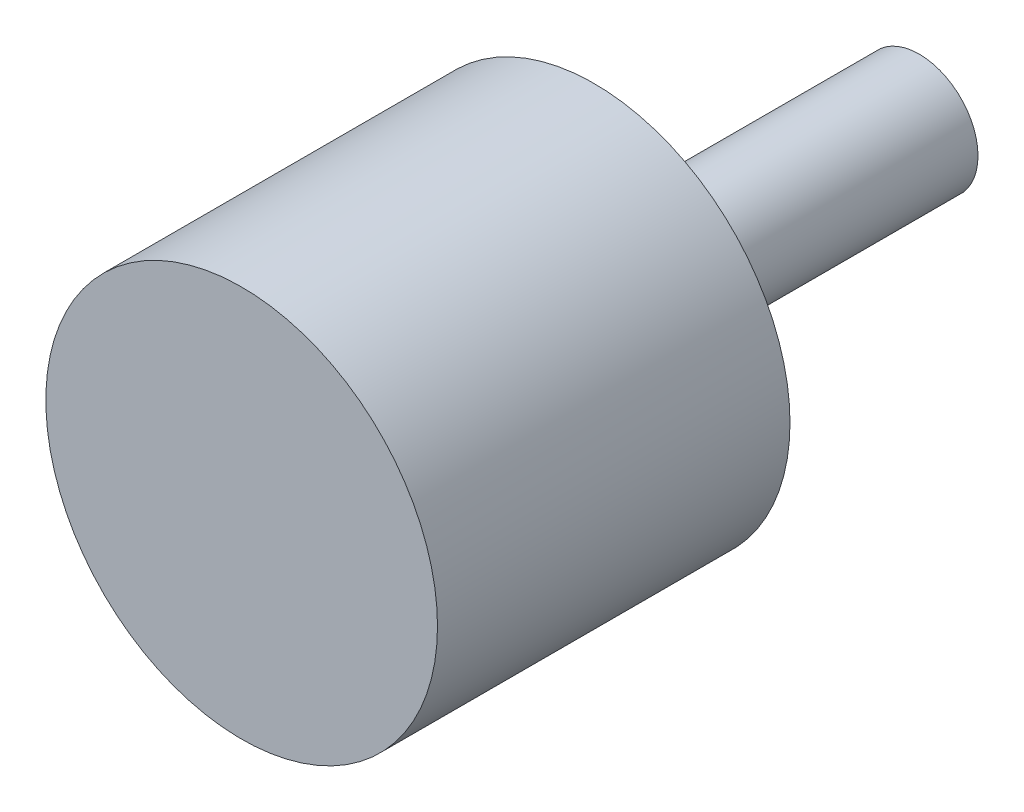
SolidWorks part; units mm, degrees
ref_plane "前视基准面" through (0, 0, 0) normal (0, 0, 1) x (1, 0, 0)
ref_plane "上视基准面" through (0, 0, 0) normal (0, 1, 0) x (1, 0, 0)
ref_plane "右视基准面" through (0, 0, 0) normal (1, 0, 0) x (0, 0, -1)
sketch "草图1" plane through (0, 0, 0) normal (0, 0, 1) x (1, 0, 0)
  circle A0 centre (0, 0) radius 5
  dimension "D1" = 10
extrude "凸台-拉伸1" add sketch "草图1" along normal blind 9
sketch "草图2" plane through (0, 0, 0) normal (0, 0, -1) x (-1, 0, 0)
  circle A0 centre (0, 0) radius 1.5
  dimension "D1" = 3
extrude "凸台-拉伸2" add sketch "草图2" along normal blind 8.3
